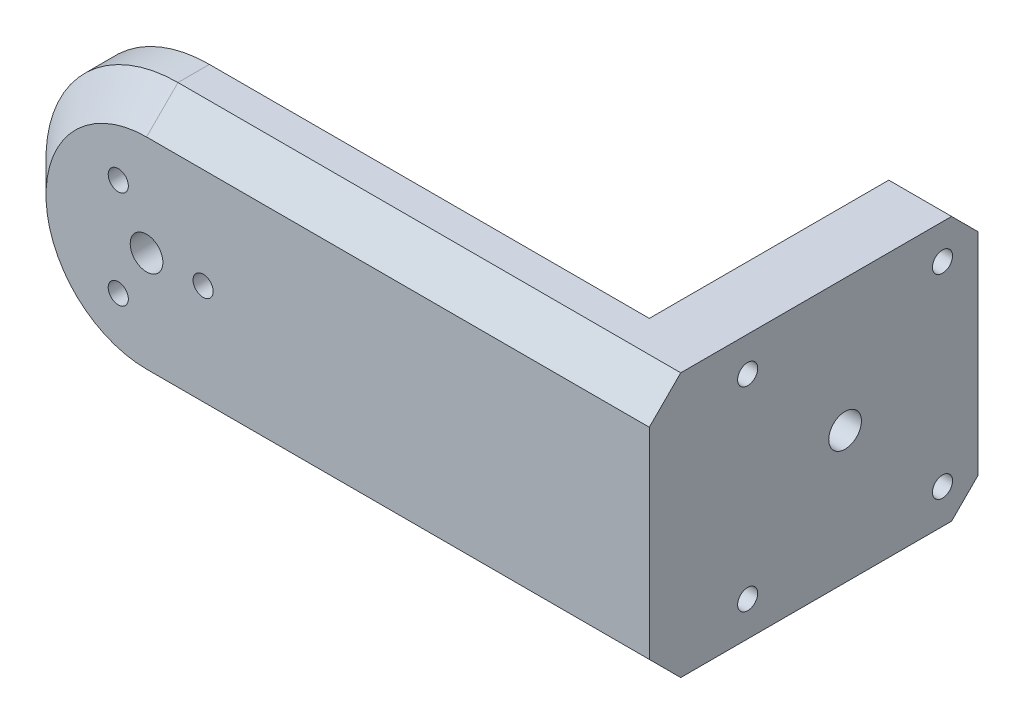
SolidWorks part; units mm, degrees
ref_plane "前视基准面" through (0, 0, 0) normal (0, 0, 1) x (1, 0, 0)
ref_plane "上视基准面" through (0, 0, 0) normal (0, 1, 0) x (1, 0, 0)
ref_plane "右视基准面" through (0, 0, 0) normal (1, 0, 0) x (0, 0, -1)
other "Configuration Table"
sketch "草图1" plane through (0, 0, 0) normal (0, 0, 1) x (1, 0, 0)
  line L0 (0, 0) -> (9, 0) construction
  line L1 (0, 0) -> (-4.5, -7.7942) construction
  circle A0 centre (0, 0) radius 12.5
  circle A1 centre (9, 0) radius 1.6
  circle A2 centre (-4.5, -7.7942) radius 1.6
  circle A3 centre (-4.5, 7.7942) radius 1.6
  point P7 (0, 9.3689)
  point P8 (0, -0.1705)
  dimension "D1" = 25
  dimension "D2" = 3.2
  dimension "D3" = 9
  dimension "D5" = 120
  dimension "D4" = 3
extrude "凸台-拉伸1" add sketch "草图1" along normal blind 11
sketch "草图2" plane through (0, 0, 11) normal (0, 0, 1) x (1, 0, 0)
  line L0 (0, 21) -> (70, 21)
  line L1 (70, 21) -> (70, -21)
  line L2 (70, -21) -> (0, -21)
  circle A0 centre (0, 0) radius 12.5
  circle A1 centre (0, 0) radius 12.5 construction
  arc A2 (0, 21) -> (0, -21) centre (0, 0) ccw
  dimension "D1" = 42
  dimension "D2" = 70
extrude "凸台-拉伸2" add sketch "草图2" against normal blind 10
sketch "草图3" plane through (70, 0, 0) normal (1, 0, 0) x (0, 0, -1)
  line L0 (-1, -21) -> (-11, -21) construction
  line L1 (-11, 21) -> (41.3, 21)
  line L2 (-11, 21) -> (-11, -21)
  line L3 (-11, -21) -> (41.3, -21)
  line L4 (41.3, 21) -> (41.3, -21)
  point P5 (-11, -21)
  dimension "D1" = 52.3
extrude "凸台-拉伸3" add sketch "草图3" along normal blind 10
sketch "草图6" plane through (0, 0, -41.3) normal (0, 0, -1) x (-1, 0, 0)
  circle A0 centre (0, 0) radius 2.6
  dimension "D1" = 5.2
extrude "切除-拉伸1" cut sketch "草图6" against normal through all
sketch "草图8" plane through (70, 0, 0) normal (-1, 0, 0) x (0, 0, 1)
  line L0 (-20.15, 21) -> (-20.15, -21) construction
  line L1 (-41.3, 21) -> (1, 21) construction
  line L2 (1, -21) -> (-41.3, -21) construction
  line L3 (-35.65, 15.5) -> (-4.65, 15.5) construction
  line L4 (-35.65, 15.5) -> (-35.65, -15.5) construction
  line L6 (-35.65, -15.5) -> (-4.65, 15.5) construction
  circle A0 centre (-35.65, 15.5) radius 1.6
  circle A1 centre (-4.65, 15.5) radius 1.6
  circle A2 centre (-4.65, -15.5) radius 1.6
  circle A3 centre (-35.65, -15.5) radius 1.6
  circle A4 centre (-20.15, 0) radius 2.6
  dimension "D6" = 3.2
  dimension "D7" = 15.5
  dimension "D9" = 5.2
  dimension "D3" = 90
  dimension "D4" = 31
  dimension "D5" = 31
  dimension "D8" = 5.5
  dimension "D1" = 2
  dimension "D2" = 2
extrude "切除-拉伸3" cut sketch "草图8" against normal through all
sketch "草图9" plane through (70, 0, 0) normal (-1, 0, 0) x (0, 0, 1)
  circle A0 centre (-20.15, 0) radius 11.5
  circle A1 centre (-20.15, 0) radius 2.6 construction
  point P2 (-31.5, 0)
  point P3 (-30.5719, 0.7503)
  dimension "D1" = 23
extrude "切除-拉伸4" cut sketch "草图9" against normal blind 3
chamfer "倒角1" distance 5 angle 45 3 edges at (40, 21, 11) (40, -21, 11) (-21, 0, 11)
chamfer "倒角2" distance 4.2 angle 45 2 edges at (75, -21, -41.3) (75, 21, -41.3)
